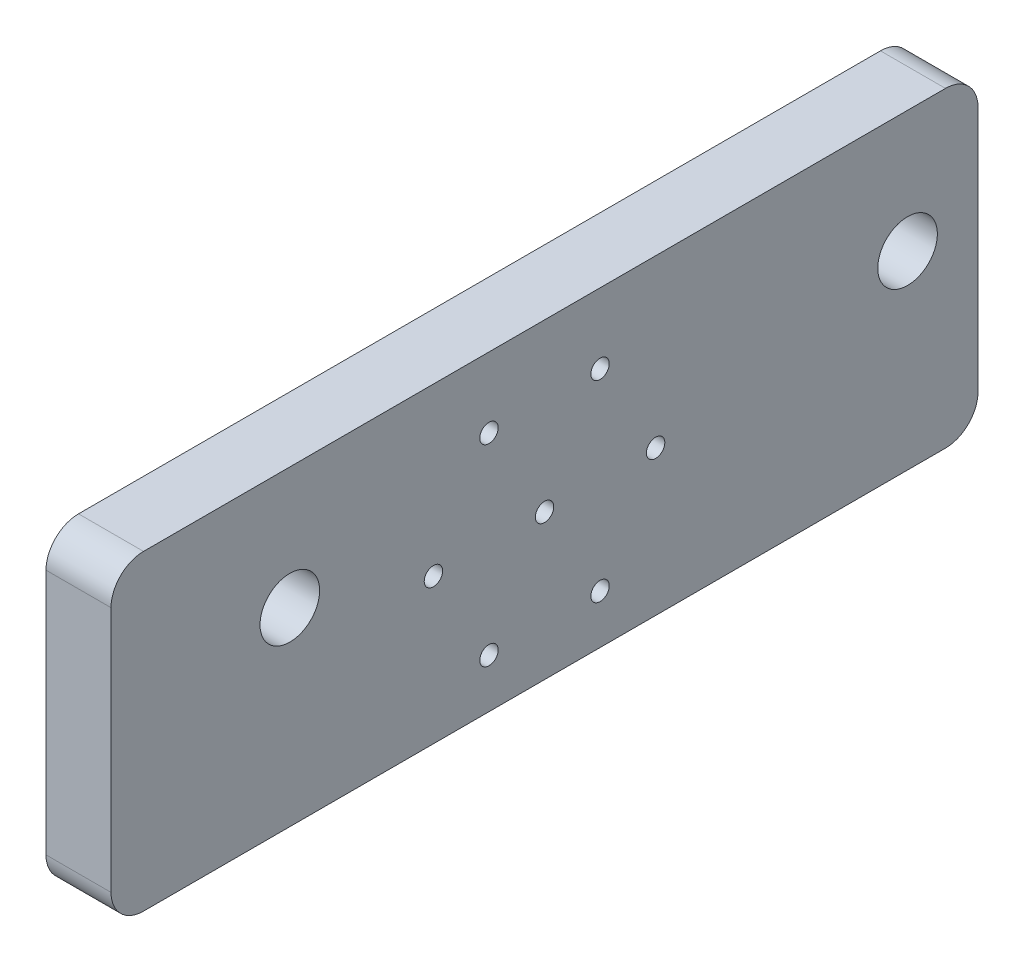
SolidWorks part; units mm, degrees
ref_plane "Front Plane" through (0, 0, 0) normal (0, 0, 1) x (1, 0, 0)
ref_plane "Top Plane" through (0, 0, 0) normal (0, 1, 0) x (1, 0, 0)
ref_plane "Right Plane" through (0, 0, 0) normal (1, 0, 0) x (0, 0, -1)
sketch "Sketch1" plane through (0, 0, 0) normal (1, 0, 0) x (0, 0, -1)
  line L0 (-10.25, -0.975) -> (10.25, -0.975) construction
  line L1 (-40, 14.375) -> (40, 14.375)
  line L2 (-40, 14.375) -> (-40, -14.375)
  line L3 (-40, -14.375) -> (40, -14.375)
  line L4 (40, 14.375) -> (40, -14.375)
  line L5 (-40, 14.375) -> (40, -14.375) construction
  line L6 (-40, -14.375) -> (40, 14.375) construction
  line L7 (5.125, -9.8518) -> (-5.125, 7.9018) construction
  line L8 (5.125, 7.9018) -> (-5.125, -9.8518) construction
  point P0 (0, 0)
  point P6 (-23.5, 3.125)
  point P7 (33.5, 3.125)
  point P8 (-10.25, -0.975)
  point P9 (10.25, -0.975)
  point P12 (0, -0.975)
  dimension "D1" = 28.75
  dimension "D2" = 80
  dimension "D3" = 11.25
  dimension "D4" = 16.5
  dimension "D5" = 6.5
  dimension "D6" = 13.4
  dimension "D7" = 20.5
  dimension "D8" = 60
  dimension "D9" = 60
extrude "Boss-Extrude1" add sketch "Sketch1" along normal blind 6
hole_wizard "M5 Clearance Hole1" positions "Sketch3" profile "Sketch2" hole size "M5" standard "ANSI Metric" end condition through all
sketch "Sketch3" plane through (0, 0, 0) normal (-1, 0, 0) x (0, 0, 1)
  point P0 (-33.5, 3.125)
  point P3 (23.5, 3.125)
sketch "Sketch2" plane through (0, 3.125, -33.5) normal (0, 1, 0) x (0, 0, 1)
  line L0 (0, 0) -> (0, 6)
  line L1 (0, 6) -> (2.75, 6)
  line L2 (2.75, 6) -> (2.75, 0)
  line L5 (2.75, 0) -> (0, 0)
  line L11 (0, -6.35) -> (0, 107.95) construction
  dimension "Thru Hole Dia." = 5.5
  dimension "Thru Hole Depth" = 6
hole_wizard "M1.6 Clearance Hole1" positions "Sketch8" profile "Sketch7" hole size "M1.6" standard "ANSI Metric" end condition through all
sketch "Sketch8" plane through (0, 0, 0) normal (-1, 0, 0) x (0, 0, 1)
  point P0 (-10.25, -0.975)
  point P3 (10.25, -0.975)
  point P7 (0, -0.975)
  point P10 (-5.125, -9.8518)
  point P12 (5.125, -9.8518)
  point P14 (5.125, 7.9018)
  point P16 (-5.125, 7.9018)
sketch "Sketch7" plane through (0, -0.975, -10.25) normal (0, 1, 0) x (0, 0, 1)
  line L0 (0, 0) -> (0, 6)
  line L1 (0, 6) -> (0.85, 6)
  line L2 (0.85, 6) -> (0.85, 0)
  line L5 (0.85, 0) -> (0, 0)
  line L11 (0, -6.35) -> (0, 107.95) construction
  dimension "Thru Hole Dia." = 1.7
  dimension "Thru Hole Depth" = 6
sketch "Sketch9" plane through (6, 0, 0) normal (1, 0, 0) x (0, 0, -1)
  line L0 (-10.25, -0.975) -> (10.25, -0.975) construction
  line L1 (-14.75, -12.8518) -> (14.75, -12.8518)
  line L2 (-14.75, -12.8518) -> (-14.75, 10.9018)
  line L3 (-14.75, 10.9018) -> (14.75, 10.9018)
  line L4 (14.75, -12.8518) -> (14.75, 10.9018)
  line L5 (-14.75, -12.8518) -> (14.75, 10.9018) construction
  line L6 (-14.75, 10.9018) -> (14.75, -12.8518) construction
  point P0 (0, -0.975)
  dimension "D1" = 3
  dimension "D2" = 4.5
extrude "Cut-Extrude1" cut sketch "Sketch9" along normal blind 2 from surface at -6 starting at face at (0, -0.975, -9.4)
fillet "Fillet1" radius 2 4 edges at (1, 10.9018, -14.75) (1, -12.8518, -14.75) (1, -12.8518, 14.75) (1, 10.9018, 14.75)
fillet "Fillet2" radius 3 4 edges at (3, -14.375, -40) (3, 14.375, -40) (3, 14.375, 40) (3, -14.375, 40)
